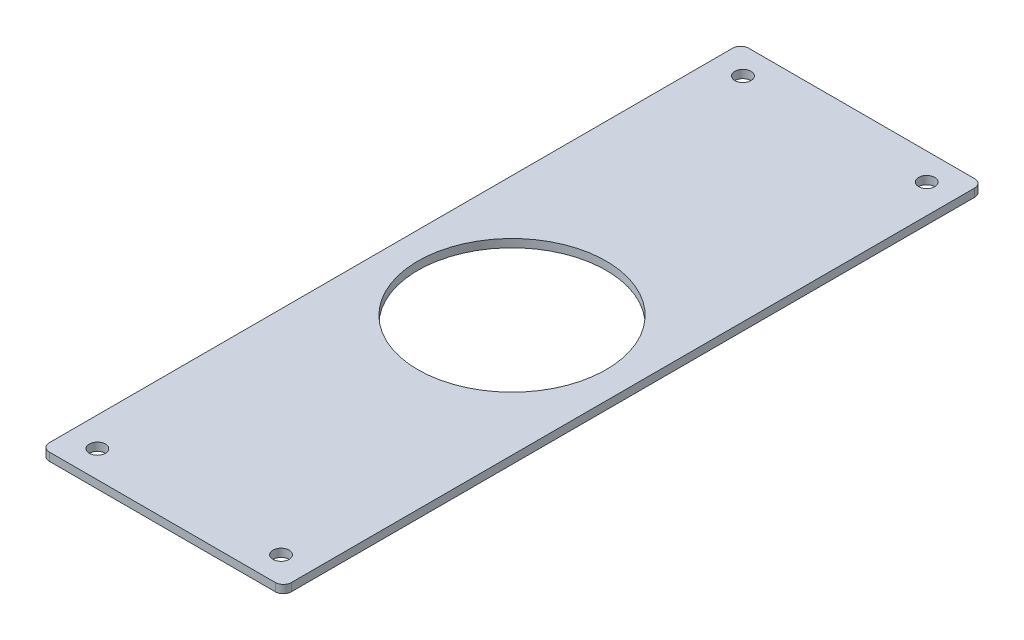
SolidWorks part; units mm, degrees
material "AISI 1045 Steel, cold drawn"
ref_plane "Front Plane" through (0, 0, 0) normal (0, 0, 1) x (1, 0, 0)
ref_plane "Top Plane" through (0, 0, 0) normal (0, 1, 0) x (1, 0, 0)
ref_plane "Right Plane" through (0, 0, 0) normal (1, 0, 0) x (0, 0, -1)
sketch "Sketch1" plane through (0, 0, 0) normal (0, 1, 0) x (1, 0, 0)
  line L0 (0, 0) -> (0, 130) construction
  line L1 (-45, -130) -> (45, -130)
  line L2 (-45, -130) -> (-45, 130)
  line L3 (-45, 130) -> (45, 130)
  line L4 (45, -130) -> (45, 130)
  line L5 (-45, -130) -> (45, 130) construction
  line L6 (-45, 130) -> (45, -130) construction
  line L7 (0, 0) -> (45, 0) construction
  circle A0 centre (0, 0) radius 35
  circle A1 centre (-34.15, 120) radius 3
  circle A2 centre (34.15, 120) radius 3
  circle A3 centre (34.15, -120) radius 3
  circle A4 centre (-34.15, -120) radius 3
  point P0 (0, 0)
  dimension "D3" = 6
  dimension "D4" = 34.15
  dimension "D5" = 120
  dimension "D6" = 70
  dimension "D1" = 90
  dimension "D2" = 260
extrude "Boss-Extrude1" add sketch "Sketch1" along normal blind 3
fillet "Fillet1" radius 3 4 edges at (-45, 1.5, -130) (45, 1.5, -130) (-45, 1.5, 130) (45, 1.5, 130)
